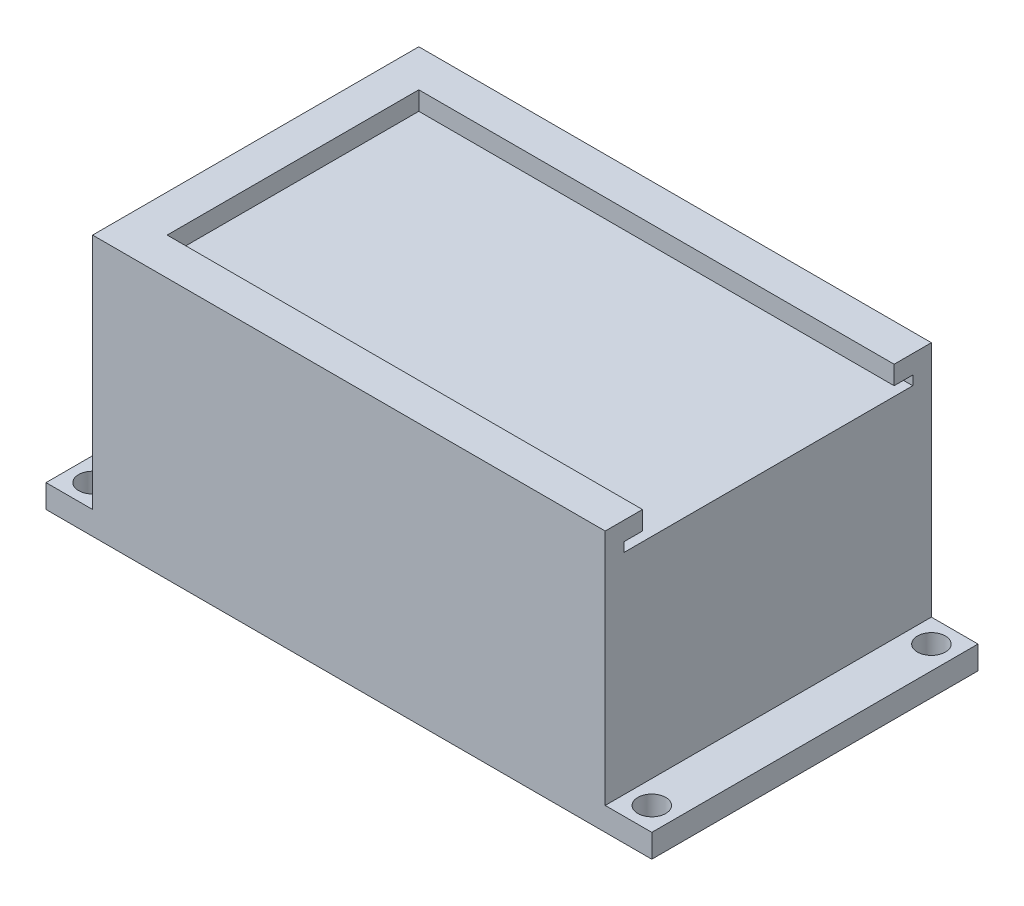
SolidWorks part; units mm, degrees
ref_plane "Front Plane" through (0, 0, 0) normal (0, 0, 1) x (1, 0, 0)
ref_plane "Top Plane" through (0, 0, 0) normal (0, 1, 0) x (1, 0, 0)
ref_plane "Right Plane" through (0, 0, 0) normal (1, 0, 0) x (0, 0, -1)
sketch "Sketch1" plane through (0, 0, 0) normal (0, 1, 0) x (1, 0, 0)
  line L1 (-165.1, 88.9) -> (0, 88.9)
  line L2 (-165.1, 88.9) -> (-165.1, 0)
  line L3 (-165.1, 0) -> (0, 0)
  line L4 (0, 88.9) -> (0, 0)
  circle A0 centre (-158.75, 6.35) radius 3.81
  circle A1 centre (-158.75, 82.55) radius 3.81
  circle A2 centre (-6.35, 82.55) radius 3.81
  circle A3 centre (-6.35, 6.35) radius 3.81
  dimension "D3" = 7.62
  dimension "D1" = 165.1
  dimension "D2" = 88.9
  dimension "D5" = 6.35
  dimension "D6" = 6.35
  dimension "D7" = 6.35
  dimension "D8" = 6.35
extrude "Boss-Extrude1" add sketch "Sketch1" along normal blind 6.35
sketch "Sketch2" plane through (0, 6.35, 0) normal (0, 1, 0) x (1, 0, 0)
  line L0 (0, 88.9) -> (-165.1, 88.9) construction
  line L1 (-152.4, 88.9) -> (-12.7, 88.9)
  line L2 (-152.4, 88.9) -> (-152.4, 0)
  line L3 (-152.4, 0) -> (-12.7, 0)
  line L4 (-12.7, 88.9) -> (-12.7, 0)
  line L5 (-165.1, 0) -> (0, 0) construction
  line L6 (0, 0) -> (0, 88.9) construction
  line L7 (-165.1, 88.9) -> (-165.1, 0) construction
  dimension "D1" = 12.7
  dimension "D2" = 12.7
extrude "Boss-Extrude2" add sketch "Sketch2" along normal blind 57.15
sketch "Sketch3" plane through (0, 0, 0) normal (0, -1, 0) x (-1, 0, 0)
  line L0 (0, 88.9) -> (165.1, 88.9) construction
  line L1 (25.4, 76.2) -> (139.7, 76.2)
  line L2 (25.4, 76.2) -> (25.4, 12.7)
  line L3 (25.4, 12.7) -> (139.7, 12.7)
  line L4 (139.7, 76.2) -> (139.7, 12.7)
  line L5 (165.1, 0) -> (0, 0) construction
  line L6 (0, 0) -> (0, 88.9) construction
  line L7 (165.1, 88.9) -> (165.1, 0) construction
  dimension "D1" = 12.7
  dimension "D2" = 12.7
  dimension "D3" = 25.4
  dimension "D4" = 25.4
extrude "Cut-Extrude1" cut sketch "Sketch3" against normal blind 50.8
sketch "Sketch5" plane through (0, 63.5, 0) normal (0, 1, 0) x (1, 0, 0)
  line L0 (-152.4, 88.9) -> (-152.4, 0) construction
  line L1 (-152.4, 0) -> (-12.7, 0)
  line L2 (-152.4, 0) -> (-152.4, 88.9)
  line L3 (-152.4, 88.9) -> (-12.7, 88.9)
  line L4 (-12.7, 0) -> (-12.7, 88.9)
  line L5 (-152.4, 0) -> (-12.7, 0) construction
  line L6 (-12.7, 88.9) -> (-152.4, 88.9) construction
  line L7 (-12.7, 0) -> (-12.7, 88.9) construction
  line L9 (-147.32, 5.08) -> (-12.7, 5.08)
  line L10 (-147.32, 5.08) -> (-147.32, 83.82)
  line L11 (-147.32, 83.82) -> (-12.7, 83.82)
  line L12 (-12.7, 5.08) -> (-12.7, 83.82)
  line M9 (-152.4, 88.9) -> (-152.4, 0)
  line M10 (-152.4, 0) -> (-12.7, 0)
  line M11 (-12.7, 0) -> (-12.7, 88.9)
  line M12 (-12.7, 88.9) -> (-152.4, 88.9)
  dimension "D1" = 5.08
  dimension "D2" = 5.08
  dimension "D3" = 5.08
extrude "Boss-Extrude3" add sketch "Sketch5" along normal blind 2.54 contours L10 L11 L9 M11 M12 M9 M10
sketch "Sketch6" plane through (0, 66.04, 0) normal (0, 1, 0) x (1, 0, 0)
  line L0 (-152.4, 88.9) -> (-152.4, 0) construction
  line L1 (-152.4, 0) -> (-12.7, 0)
  line L2 (-152.4, 0) -> (-152.4, 88.9)
  line L3 (-152.4, 88.9) -> (-12.7, 88.9)
  line L4 (-12.7, 0) -> (-12.7, 88.9)
  line L5 (-12.7, 88.9) -> (-152.4, 88.9) construction
  line L6 (-152.4, 0) -> (-12.7, 0) construction
  line L7 (-12.7, 5.08) -> (-12.7, 83.82) construction
  line L8 (-147.32, 83.82) -> (-12.7, 83.82) construction
  line L9 (-142.24, 10.16) -> (-12.7, 10.16)
  line L10 (-142.24, 10.16) -> (-142.24, 78.74)
  line L11 (-142.24, 78.74) -> (-12.7, 78.74)
  line L12 (-12.7, 10.16) -> (-12.7, 78.74)
  line L13 (-147.32, 5.08) -> (-147.32, 83.82) construction
  line M9 (-147.32, 5.08) -> (-147.32, 83.82)
  line M10 (-147.32, 83.82) -> (-12.7, 83.82)
  line M11 (-12.7, 83.82) -> (-12.7, 88.9)
  line M12 (-12.7, 88.9) -> (-152.4, 88.9)
  line M13 (-152.4, 88.9) -> (-152.4, 0)
  line M14 (-152.4, 0) -> (-12.7, 0)
  line M15 (-12.7, 0) -> (-12.7, 5.08)
  line M16 (-12.7, 5.08) -> (-147.32, 5.08)
  dimension "D1" = 10.16
  dimension "D2" = 5.08
  dimension "D3" = 5.08
extrude "Boss-Extrude4" add sketch "Sketch6" along normal blind 5.08 contours L10 L11 L4 L9 M10 M9 M16 | M16 M9 M10 M11 M12 M13 M14 M15
